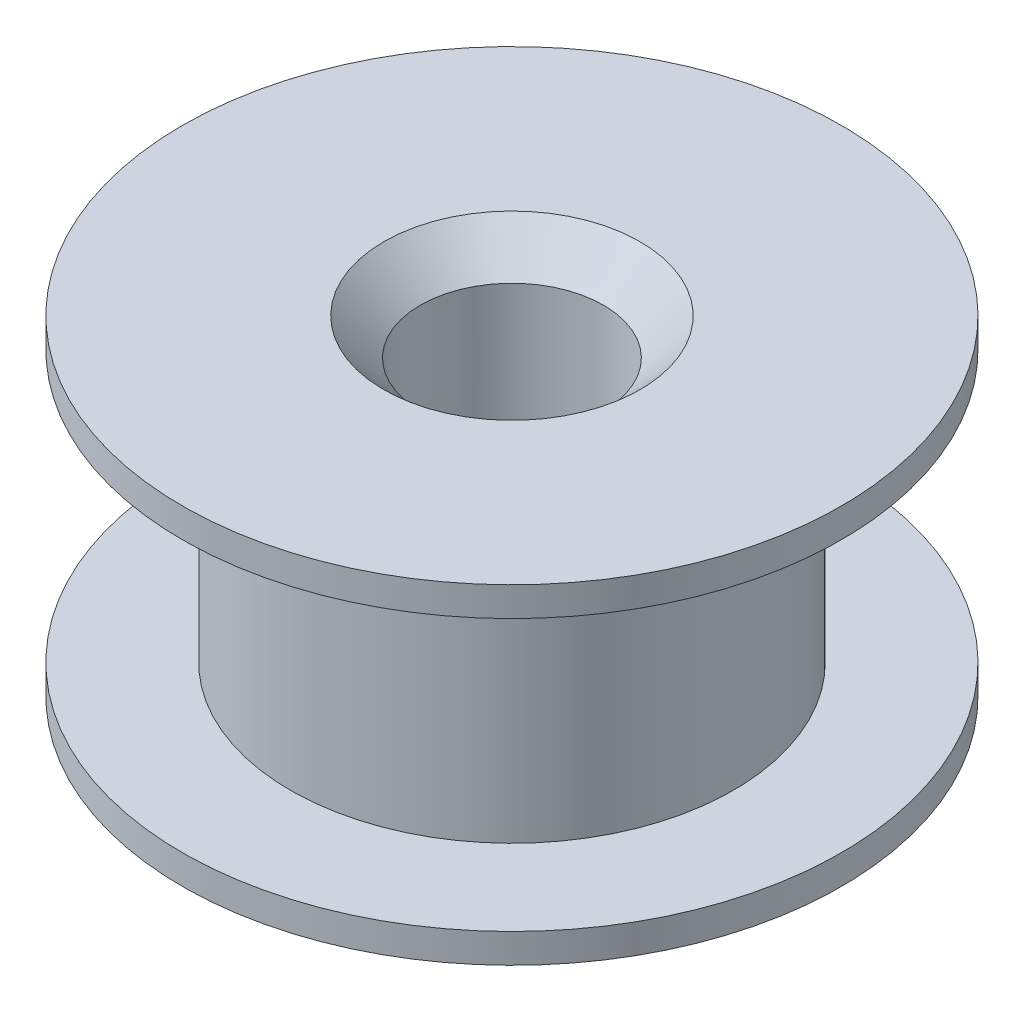
SolidWorks part; units mm, degrees
ref_plane "Спереди" through (0, 0, 0) normal (0, 0, 1) x (1, 0, 0)
ref_plane "Сверху" through (0, 0, 0) normal (0, 1, 0) x (1, 0, 0)
ref_plane "Справа" through (0, 0, 0) normal (1, 0, 0) x (0, 0, -1)
sketch "Эскиз1" plane through (0, 0, 0) normal (0, 0, 1) x (1, 0, 0)
  line L0 (-2.5, 0) -> (-9, 0)
  line L1 (-9, 0) -> (-9, 0.8)
  line L2 (-9, 0.8) -> (-6.05, 0.8)
  line L3 (-6.05, 0.8) -> (-6.05, 8.2)
  line L4 (-6.05, 8.2) -> (-9, 8.2)
  line L5 (-9, 8.2) -> (-9, 9)
  line L6 (-9, 9) -> (-2.5, 9)
  line L7 (0, 9) -> (0, 0) construction
  line L8 (-2.5, 9) -> (-2.5, 0)
  line L9 (-2.5, 9) -> (0, 9) construction
  line L10 (0, 0) -> (-2.5, 0) construction
  dimension "D1" = 18
  dimension "D2" = 12.1
  dimension "D3" = 9
  dimension "D4" = 7.4
  dimension "D5" = 5
revolve "Повернуть1" add sketch "Эскиз1" angle 360 about L7
chamfer "Фаска1" distance 1 angle 45 1 edges at (-2.5, 9, 0)
chamfer "Фаска2" distance 1 angle 45 1 edges at (-2.5, 0, 0)
sketch "Эскиз2" plane through (0, 9, 0) normal (0, 1, 0) x (1, 0, 0)
  line L0 (9, 0) -> (-9, 0) construction
  circle A0 centre (0, 0) radius 9 construction
ref_plane "Плоскость1" through (0, 0, 0) normal (0, 0, -1) x (-1, 0, 0)
sketch "Эскиз3" plane through (0, 0, 0) normal (0, 0, -1) x (-1, 0, 0)
  line L0 (-9, 0) -> (9, 0) construction
  line L1 (-9, 0) -> (9, 0) construction
  line L2 (9, 9) -> (-9, 9) construction
  line L3 (9, 9) -> (-9, 9) construction
  line L4 (0, 9) -> (0, 0) construction
  line L5 (0, 4.5) -> (-9, 4.5) construction
  line L6 (-9, 0) -> (-9, 9) construction
ref_plane "A" through (0, 4.5, 0) normal (0, 1, 0) x (1, 0, 0)
